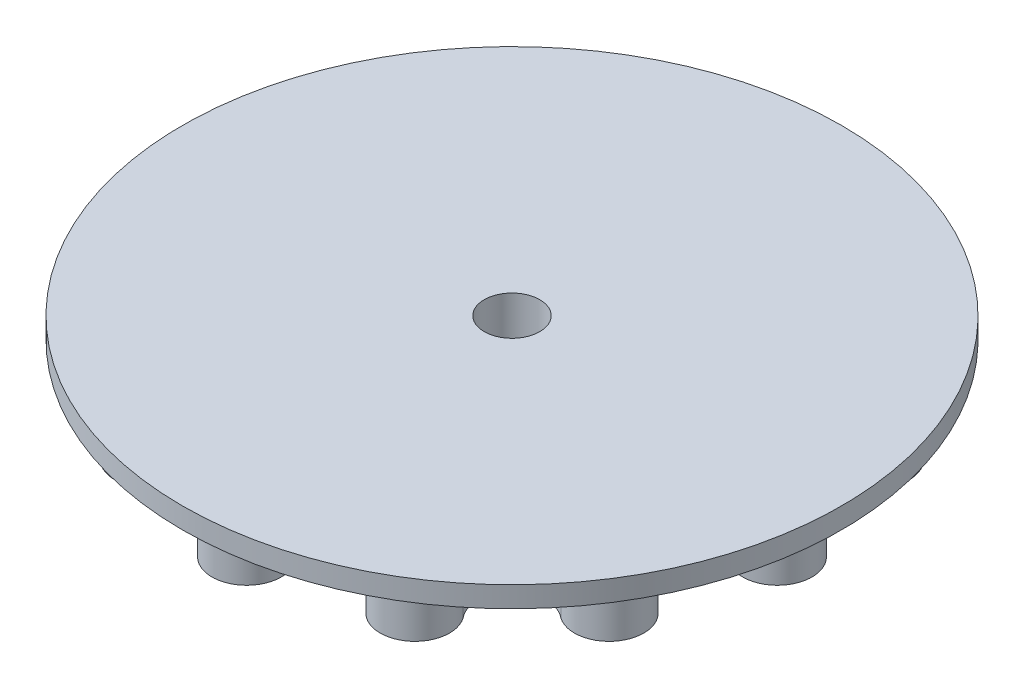
SolidWorks part; units mm, degrees
material "1060 Alloy"
ref_plane "Front" through (0, 0, 0) normal (0, 0, 1) x (1, 0, 0)
ref_plane "Top" through (0, 0, 0) normal (0, 1, 0) x (1, 0, 0)
ref_plane "Right" through (0, 0, 0) normal (1, 0, 0) x (0, 0, -1)
sketch "Sketch1" plane through (0, 0, 0) normal (0, 1, 0) x (1, 0, 0)
  line L4 (-55, 0) -> (55, 0) construction
  circle A0 centre (0, 0) radius 38.25
  circle A1 centre (0, 38.25) radius 5
  circle A32 centre (9.8998, 36.9467) radius 5
  circle A33 centre (19.125, 33.1255) radius 5
  circle A34 centre (27.0468, 27.0468) radius 5
  circle A35 centre (33.1255, 19.125) radius 5
  circle A36 centre (36.9467, 9.8998) radius 5
  circle A37 centre (38.25, 0) radius 5
  circle A38 centre (36.9467, -9.8998) radius 5
  circle A39 centre (33.1255, -19.125) radius 5
  circle A40 centre (27.0468, -27.0468) radius 5
  circle A41 centre (19.125, -33.1255) radius 5
  circle A42 centre (9.8998, -36.9467) radius 5
  circle A43 centre (0, -38.25) radius 5
  circle A44 centre (-9.8998, -36.9467) radius 5
  circle A45 centre (-19.125, -33.1255) radius 5
  circle A46 centre (-27.0468, -27.0468) radius 5
  circle A47 centre (-33.1255, -19.125) radius 5
  circle A48 centre (-36.9467, -9.8998) radius 5
  circle A49 centre (-38.25, 0) radius 5
  circle A50 centre (-36.9467, 9.8998) radius 5
  circle A51 centre (-33.1255, 19.125) radius 5
  circle A52 centre (-27.0468, 27.0468) radius 5
  circle A53 centre (-19.125, 33.1255) radius 5
  circle A54 centre (-9.8998, 36.9467) radius 5
  point P29 (0, 0)
  point P47 (0.0805, -0.2479)
  point P56 (0, 0)
  dimension "D1" = 76.5
  dimension "D2" = 10
  dimension "D3" = 24
  dimension "D4" = 38.25
  dimension "D5" = 27.0468
extrude "Boss-Extrude1" add sketch "Sketch1" along normal blind 8 contours A54 A53 A52 A51 A50 A49 A48 A47 A46 A45 A44 A43 A42 A41 A40 A39 A38 A37 A36 A35 A34 A33 A32 A1 | A0 A1 | A54 A1 A32 A0 | A0 A53 | A54 A53 A0 A52 | A0 A51 | A52 A51 A0 A50 | A50 A49 A0 A48 | A0 A49 | A48 A47 A0 A46 | A0 A47 | A46 A45 A0 A44 | A0 A45 | A44 A43 A0 A42 | A0 A43 | A42 A41 A0 A40 | A0 A41 | A40 A39 A0 A38 | A0 A39 | A38 A37 A0 A36 | A0 A37 | A36 A35 A0 A34 | A0 A35 | A34 A33 A0 A32 | A0 A33
sketch "Sketch3" plane through (0, 8, 0) normal (0, 1, 0) x (1, 0, 0)
  circle A0 centre (0, 0) radius 47.5
  dimension "D1" = 95
extrude "Boss-Extrude2" add sketch "Sketch3" along normal blind 3
sketch "Sketch4" plane through (0, 11, 0) normal (0, 1, 0) x (1, 0, 0)
  circle A0 centre (0, 0) radius 4
  dimension "D1" = 8
extrude "Cut-Extrude1" cut sketch "Sketch4" against normal blind 30
